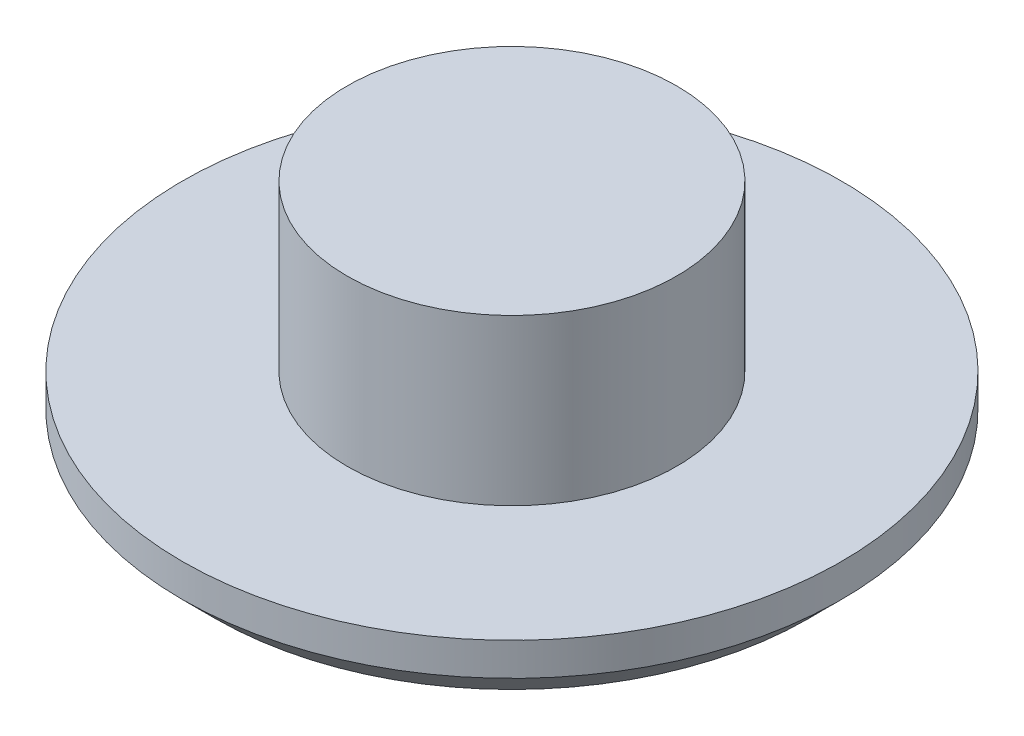
SolidWorks part; units mm, degrees
ref_plane "Front Plane" through (0, 0, 0) normal (0, 0, 1) x (1, 0, 0)
ref_plane "Top Plane" through (0, 0, 0) normal (0, 1, 0) x (1, 0, 0)
ref_plane "Right Plane" through (0, 0, 0) normal (1, 0, 0) x (0, 0, -1)
sketch "Sketch1" plane through (0, 0, 0) normal (0, 1, 0) x (1, 0, 0)
  circle A0 centre (0, 0) radius 12.7
  point P2 (0, 0)
  dimension "D1" = 25.4
extrude "Boss-Extrude1" add sketch "Sketch1" along normal blind 2.54
sketch "Sketch2" plane through (0, 2.54, 0) normal (0, 1, 0) x (1, 0, 0)
  circle A0 centre (0, 0) radius 6.35
  point P2 (0, 0)
  dimension "D1" = 12.7
extrude "Boss-Extrude2" add sketch "Sketch2" along normal blind 6.35
chamfer "Chamfer1" distance 1.27 angle 45 1 edges at (0, 0, 12.7)
